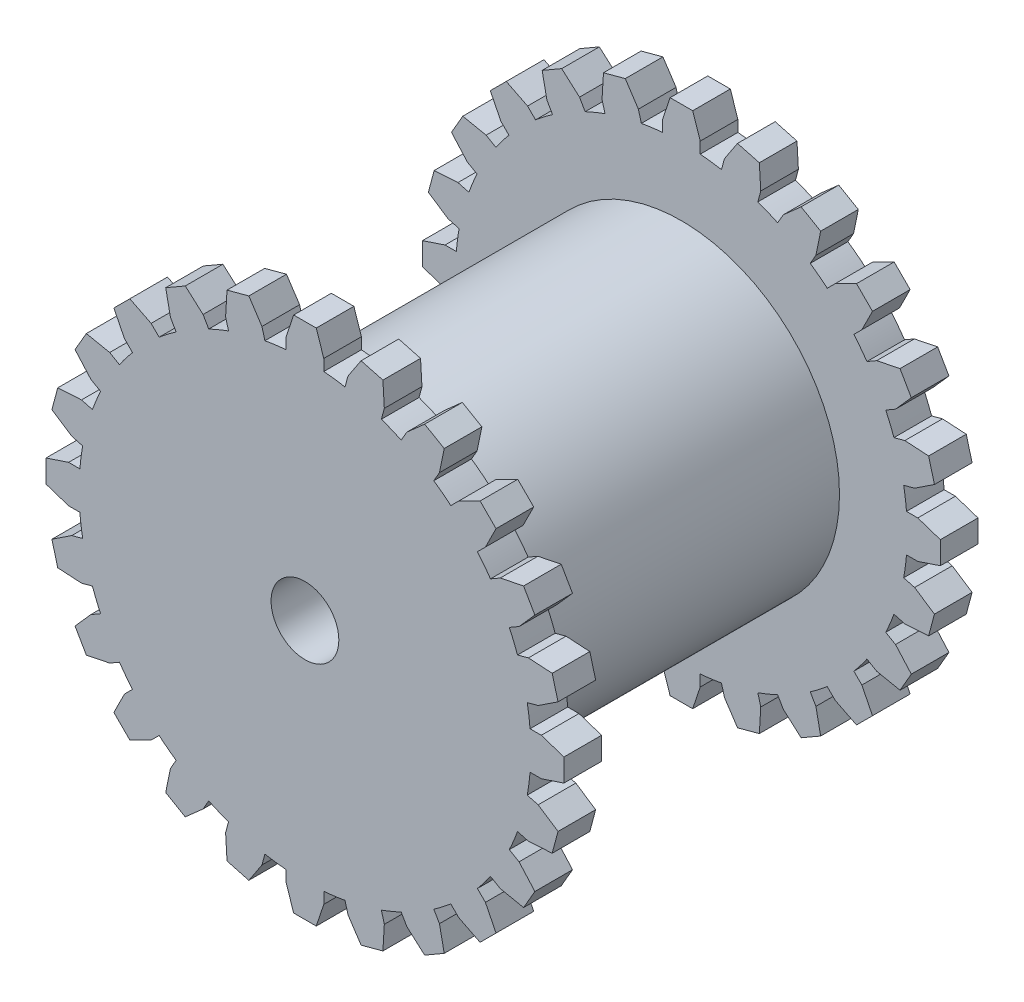
SolidWorks part; units mm, degrees
ref_plane "Front Plane" through (0, 0, 0) normal (0, 0, 1) x (1, 0, 0)
ref_plane "Top Plane" through (0, 0, 0) normal (0, 1, 0) x (1, 0, 0)
ref_plane "Right Plane" through (0, 0, 0) normal (1, 0, 0) x (0, 0, -1)
sketch "Sketch1" plane through (0, 0, 0) normal (0, 0, 1) x (1, 0, 0)
  circle A0 centre (0, 0) radius 4.5
  circle A1 centre (0, 0) radius 30
  dimension "D1" = 60
  dimension "D2" = 9
extrude "Boss-Extrude1" add sketch "Sketch1" along normal blind 5
sketch "Sketch2" plane through (0, 0, 0) normal (0, 0, 1) x (1, 0, 0)
  line L0 (0, 299.8374) -> (0, 0) construction
  line L1 (-1.5, 34.3957) -> (1.5, 34.3957)
  line L2 (1.5, 34.3957) -> (2.5, 31.3957)
  line L3 (2.5, 31.3957) -> (2.5, 29.8957)
  line L4 (-1.5, 34.3957) -> (-2.5, 31.3957)
  line L5 (-2.5, 31.3957) -> (-2.5, 29.8957)
  circle A0 centre (0, 0) radius 30
  circle A1 centre (0, 0) radius 30 construction
  point P5 (0, 34.3957)
  dimension "D6" = 60
  dimension "D1" = 3
  dimension "D2" = 5
  dimension "D3" = 1.5
  dimension "D4" = 3
  dimension "D5" = 3
  dimension "D7" = 1
extrude "Boss-Extrude2" add sketch "Sketch2" along normal blind 5
pattern_circular "CirPattern1" count 24 over 360 about axis through (0, 0, 0) along (0, 0, 1) of "Boss-Extrude2"
sketch "Sketch3" plane through (0, 0, 0) normal (0, 0, 1) x (1, 0, 0)
  circle A0 centre (0, 0) radius 21
  circle A1 centre (0, 0) radius 4.5
  dimension "D1" = 42
  dimension "D2" = 9
extrude "Boss-Extrude5" add sketch "Sketch3" against normal blind 22.5 contours A1 | A0
mirror "Mirror2" about plane through (0, 0, -22.5) normal (0, 0, 1) of bodies 106
